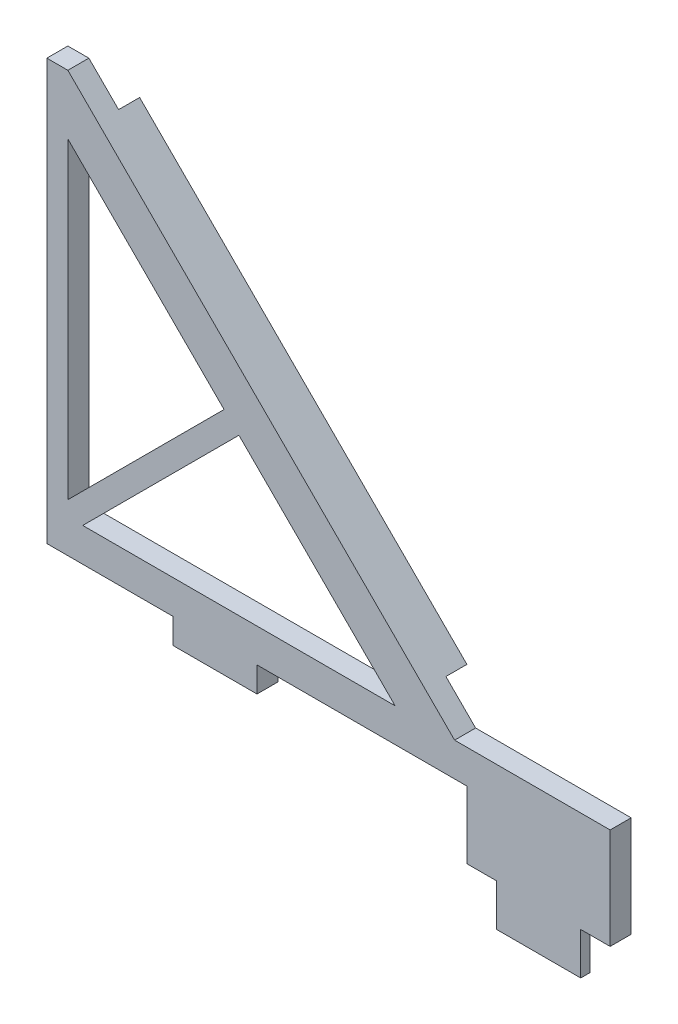
SolidWorks part; units mm, degrees
ref_plane "Front Plane" through (0, 0, 0) normal (0, 0, 1) x (1, 0, 0)
ref_plane "Top Plane" through (0, 0, 0) normal (0, 1, 0) x (1, 0, 0)
ref_plane "Right Plane" through (0, 0, 0) normal (1, 0, 0) x (0, 0, -1)
sketch "Sketch2" plane through (0, 0, 0) normal (0, 0, 1) x (1, 0, 0)
  line L0 (0, 0) -> (12.7, 0)
  line L1 (12.7, 0) -> (12.7, 6.35)
  line L2 (12.7, 6.35) -> (17.145, 6.35)
  line L3 (17.145, 6.35) -> (17.145, 21.59)
  line L5 (0, 0) -> (0, 6.35)
  line L6 (0, 6.35) -> (-4.445, 6.35)
  line L7 (-4.445, 6.35) -> (-4.445, 16.51)
  line L11 (-64.77, 80.01) -> (-67.945, 80.01)
  line L13 (-48.895, 16.51) -> (-48.895, 12.7)
  line L14 (-67.945, 80.01) -> (-67.945, 16.51)
  line L15 (-67.945, 16.51) -> (-48.895, 16.51)
  line L18 (-48.895, 12.7) -> (-36.195, 12.7)
  line L19 (-36.195, 12.7) -> (-36.195, 16.51)
  line L20 (-36.195, 16.51) -> (-4.445, 16.51)
  line L21 (17.145, 21.59) -> (-6.35, 21.59)
  line L22 (-6.35, 21.59) -> (-64.77, 80.01)
  line L23 (-64.77, 71.0297) -> (-64.77, 23.8351)
  line L24 (-62.5249, 21.59) -> (-15.3303, 21.59)
  line L25 (-15.3303, 21.59) -> (-38.9276, 45.1873)
  line L26 (-41.1727, 47.4324) -> (-64.77, 23.8351)
  line L27 (-38.9276, 45.1873) -> (-62.5249, 21.59)
  line L28 (-41.1727, 47.4324) -> (-64.77, 71.0297)
  point P16 (14.9225, 6.35)
  dimension "D1" = 63.5
  dimension "D2" = 12.7
  dimension "D3" = 4.445
  dimension "D4" = 4.445
  dimension "D5" = 6.35
  dimension "D6" = 6.35
  dimension "D7" = 45
  dimension "D8" = 6.35
  dimension "D9" = 5.08
  dimension "D10" = 3.175
  dimension "D11" = 6.35
  dimension "D12" = 15.24
  dimension "D13" = 6.35
  dimension "D14" = 31.75
  dimension "D15" = 12.7
  dimension "D16" = 3.81
  dimension "D17" = 3.175
extrude "Boss-Extrude1" add sketch "Sketch2" along normal blind 3.175
sketch "Sketch3" plane through (0, 0, 0) normal (0, 0, -1) x (-1, 0, 0)
  line L1 (-12.7, 0) -> (0, 0)
  line L2 (-12.7, 0) -> (-12.7, 6.35)
  line L3 (-12.7, 6.35) -> (0, 6.35)
  line L4 (0, 0) -> (0, 6.35)
extrude "Cut-Extrude1" cut sketch "Sketch3" against normal blind 1.778
sketch "Sketch4" plane through (0, 0, 0) normal (0, 0, -1) x (-1, 0, 0)
  line L0 (15.3303, 21.59) -> (64.77, 71.0297)
  line L1 (64.77, 71.0297) -> (62.929, 72.8707)
  line L2 (62.929, 72.8707) -> (13.4893, 23.431)
  line L3 (13.4893, 23.431) -> (15.3303, 21.59)
  line L4 (10.8401, 26.0801) -> (12.6811, 24.2392)
  line L5 (6.35, 21.59) -> (64.77, 80.01) construction
  line L6 (12.6811, 24.2392) -> (62.1208, 73.6789)
  line L7 (62.1208, 73.6789) -> (60.2799, 75.5199)
  line L8 (60.2799, 75.5199) -> (10.8401, 26.0801)
  dimension "D1" = 1.143
extrude "Boss-Extrude2" add sketch "Sketch4" along normal blind 3.175
